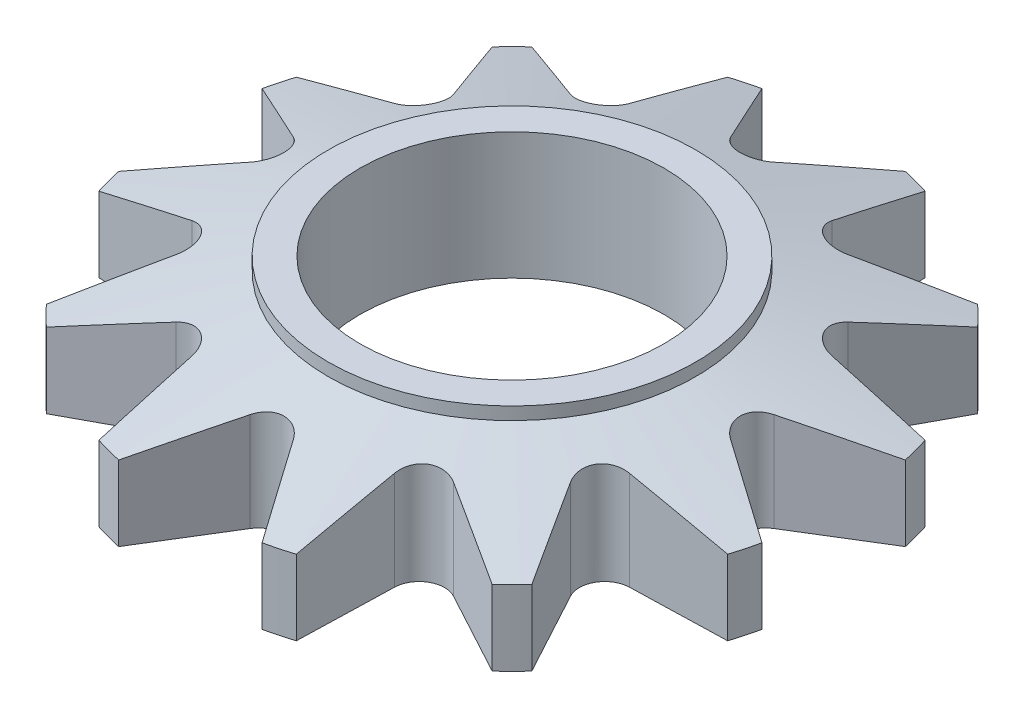
SolidWorks part; units mm, degrees
ref_plane "Front Plane" through (0, 0, 0) normal (0, 0, 1) x (1, 0, 0)
ref_plane "Top Plane" through (0, 0, 0) normal (0, 1, 0) x (1, 0, 0)
ref_plane "Right Plane" through (0, 0, 0) normal (1, 0, 0) x (0, 0, -1)
sketch "Sketch1" plane through (0, 0, 0) normal (0, 1, 0) x (1, 0, 0)
  circle A0 centre (0, 0) radius 260
  circle A1 centre (0, 0) radius 120
extrude "Boss-Extrude1" add sketch "Sketch1" along normal mid plane 90
sketch "Sketch2" plane through (0, 0, 0) normal (0, 1, 0) x (1, 0, 0)
  circle A0 centre (0, 0) radius 145
  circle A1 centre (0, 0) radius 120 construction
  circle A2 centre (0, 0) radius 120
  dimension "D1" = 290
extrude "Boss-Extrude3" add sketch "Sketch2" along normal blind 55
sketch "Sketch3" plane through (0, 0, 0) normal (0, 1, 0) x (1, 0, 0)
  line L0 (0, 260) -> (0, -260) construction
  line L1 (-260, 0) -> (260, 0) construction
  line L2 (17.0332, 189.5181) -> (56.5731, 253.7705)
  line L3 (-17.0332, 189.5181) -> (-56.5731, 253.7705)
  circle A0 centre (0, 0) radius 260 construction
  arc A1 (-17.0332, 189.5181) -> (17.0332, 189.5181) centre (0, 200) ccw
  dimension "D2" = 200
sketch "Sketch4" plane through (0, 0, 0) normal (0, 1, 0) x (1, 0, 0)
  line L0 (-17.0332, 189.5181) -> (-56.5731, 253.7705) construction
  line L1 (17.0332, 189.5181) -> (56.5731, 253.7705) construction
  line L2 (-17.0332, 189.5181) -> (-56.5731, 253.7705)
  line L3 (17.0332, 189.5181) -> (56.5731, 253.7705)
  line L4 (109.5102, 155.6109) -> (175.879, 191.4852)
  line L5 (80.0079, 172.6441) -> (77.8916, 248.0583)
  line L6 (172.6441, 80.0079) -> (248.0583, 77.8916)
  line L7 (155.6109, 109.5102) -> (191.4852, 175.879)
  line L8 (189.5181, -17.0332) -> (253.7705, -56.5731)
  line L9 (189.5181, 17.0332) -> (253.7705, 56.5731)
  line L10 (155.6109, -109.5102) -> (191.4852, -175.879)
  line L11 (172.6441, -80.0079) -> (248.0583, -77.8916)
  line L12 (80.0079, -172.6441) -> (77.8916, -248.0583)
  line L13 (109.5102, -155.6109) -> (175.879, -191.4852)
  line L14 (-17.0332, -189.5181) -> (-56.5731, -253.7705)
  line L15 (17.0332, -189.5181) -> (56.5731, -253.7705)
  line L16 (-109.5102, -155.6109) -> (-175.879, -191.4852)
  line L17 (-80.0079, -172.6441) -> (-77.8916, -248.0583)
  line L18 (-172.6441, -80.0079) -> (-248.0583, -77.8916)
  line L19 (-155.6109, -109.5102) -> (-191.4852, -175.879)
  line L20 (-189.5181, 17.0332) -> (-253.7705, 56.5731)
  line L21 (-189.5181, -17.0332) -> (-253.7705, -56.5731)
  line L22 (-155.6109, 109.5102) -> (-191.4852, 175.879)
  line L23 (-172.6441, 80.0079) -> (-248.0583, 77.8916)
  line L24 (-80.0079, 172.6441) -> (-77.8916, 248.0583)
  line L25 (-109.5102, 155.6109) -> (-175.879, 191.4852)
  arc A0 (-56.5731, 253.7705) -> (56.5731, 253.7705) centre (0, 0) cw
  arc A1 (-17.0332, 189.5181) -> (17.0332, 189.5181) centre (0, 200) ccw construction
  arc A2 (-17.0332, 189.5181) -> (17.0332, 189.5181) centre (0, 200) ccw
  arc A3 (77.8916, 248.0583) -> (175.879, 191.4852) centre (0, 0) cw
  arc A4 (80.0079, 172.6441) -> (109.5102, 155.6109) centre (100, 173.2051) ccw
  arc A5 (191.4852, 175.879) -> (248.0583, 77.8916) centre (0, 0) cw
  arc A6 (155.6109, 109.5102) -> (172.6441, 80.0079) centre (173.2051, 100) ccw
  arc A7 (253.7705, 56.5731) -> (253.7705, -56.5731) centre (0, 0) cw
  arc A8 (189.5181, 17.0332) -> (189.5181, -17.0332) centre (200, 0) ccw
  arc A9 (248.0583, -77.8916) -> (191.4852, -175.879) centre (0, 0) cw
  arc A10 (172.6441, -80.0079) -> (155.6109, -109.5102) centre (173.2051, -100) ccw
  arc A11 (175.879, -191.4852) -> (77.8916, -248.0583) centre (0, 0) cw
  arc A12 (109.5102, -155.6109) -> (80.0079, -172.6441) centre (100, -173.2051) ccw
  arc A13 (56.5731, -253.7705) -> (-56.5731, -253.7705) centre (0, 0) cw
  arc A14 (17.0332, -189.5181) -> (-17.0332, -189.5181) centre (0, -200) ccw
  arc A15 (-77.8916, -248.0583) -> (-175.879, -191.4852) centre (0, 0) cw
  arc A16 (-80.0079, -172.6441) -> (-109.5102, -155.6109) centre (-100, -173.2051) ccw
  arc A17 (-191.4852, -175.879) -> (-248.0583, -77.8916) centre (0, 0) cw
  arc A18 (-155.6109, -109.5102) -> (-172.6441, -80.0079) centre (-173.2051, -100) ccw
  arc A19 (-253.7705, -56.5731) -> (-253.7705, 56.5731) centre (0, 0) cw
  arc A20 (-189.5181, -17.0332) -> (-189.5181, 17.0332) centre (-200, 0) ccw
  arc A21 (-248.0583, 77.8916) -> (-191.4852, 175.879) centre (0, 0) cw
  arc A22 (-172.6441, 80.0079) -> (-155.6109, 109.5102) centre (-173.2051, 100) ccw
  arc A23 (-175.879, 191.4852) -> (-77.8916, 248.0583) centre (0, 0) cw
  arc A24 (-109.5102, 155.6109) -> (-80.0079, 172.6441) centre (-100, 173.2051) ccw
  dimension "D1" = 260
  dimension "D2" = 12
extrude "Cut-Extrude1" cut sketch "Sketch4" against normal through all and the other way through all
sketch "Sketch8" plane through (0, 0, 0) normal (0, 0, 1) x (1, 0, 0)
  line L0 (0, 0) -> (0, 99.1278)
sketch "Sketch9" plane through (0, 0, 0) normal (1, 0, 0) x (0, 0, -1)
  line L0 (145, 45) -> (312.9423, 45)
  line L1 (312.9423, 45) -> (312.9423, 0)
  line L2 (126.5218, 0) -> (-126.5218, 0) construction
  line L3 (312.9423, 0) -> (145, 45)
  dimension "D1" = 15
revolve "Cut-Revolve2" cut sketch "Sketch9" angle 360 about L0
scale "Scale2" scale about centroid uniform scaling yes scale factor 0.4
